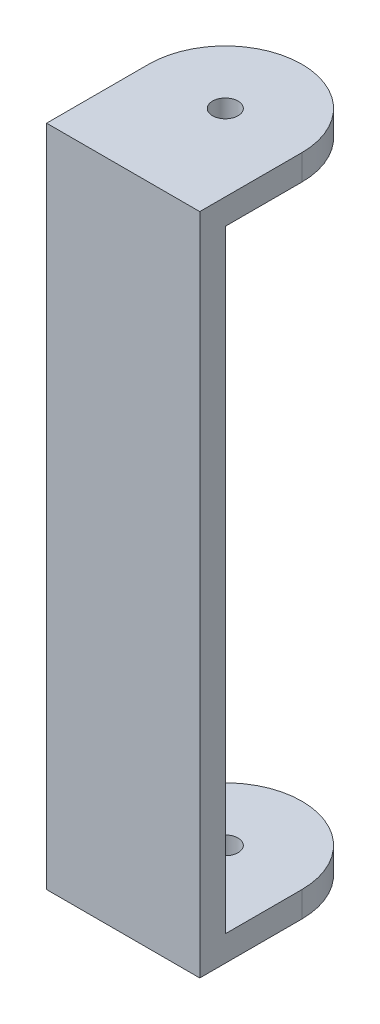
SolidWorks part; units mm, degrees
ref_plane "Front" through (0, 0, 0) normal (0, 0, 1) x (1, 0, 0)
ref_plane "Top" through (0, 0, 0) normal (0, 1, 0) x (1, 0, 0)
ref_plane "Right" through (0, 0, 0) normal (1, 0, 0) x (0, 0, -1)
sketch "Sketch1" plane through (0, 0, 0) normal (0, 1, 0) x (1, 0, 0)
  line L0 (-19.05, -25.4) -> (19.05, -25.4)
  line L1 (19.05, -25.4) -> (19.05, 0)
  line L2 (-19.05, -25.4) -> (-19.05, 0)
  circle A0 centre (0, 0) radius 3.175
  arc A1 (19.05, 0) -> (-19.05, 0) centre (0, 0) ccw
  dimension "D1" = 6.35
  dimension "D2" = 19.05
  dimension "D3" = 25.4
extrude "Extrude1" add sketch "Sketch1" along normal mid plane 165.1
sketch "Sketch2" plane through (19.05, 0, 0) normal (1, 0, 0) x (0, 0, -1)
  line L0 (19.05, -82.55) -> (19.05, 82.55) construction
  line L1 (-19.05, 76.2) -> (19.05, 76.2)
  line L2 (-19.05, 76.2) -> (-19.05, -76.2)
  line L3 (-19.05, -76.2) -> (19.05, -76.2)
  line L4 (19.05, 76.2) -> (19.05, -76.2)
  line L5 (0, 0) -> (-54.4207, 0) construction
  line L6 (-25.4, 82.55) -> (-25.4, -82.55) construction
  line L7 (-25.4, -82.55) -> (0, -82.55) construction
  point P6 (-19.05, 0)
  dimension "D1" = 6.35
  dimension "D2" = 6.35
extrude "Extrude2" cut sketch "Sketch2" against normal through all
